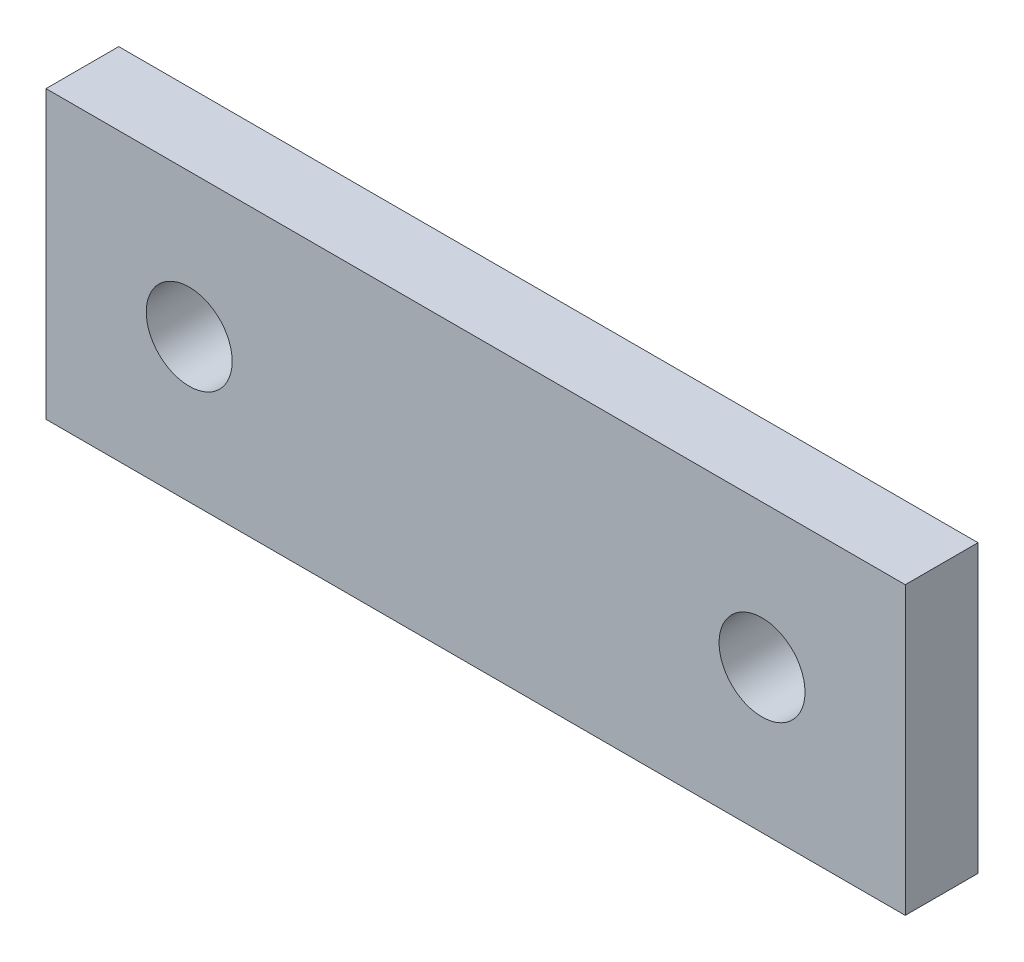
SolidWorks part; units mm, degrees
ref_plane "Front Plane" through (0, 0, 0) normal (0, 0, 1) x (1, 0, 0)
ref_plane "Top Plane" through (0, 0, 0) normal (0, 1, 0) x (1, 0, 0)
ref_plane "Right Plane" through (0, 0, 0) normal (1, 0, 0) x (0, 0, -1)
sketch "Sketch1" plane through (0, 0, 0) normal (0, 0, 1) x (1, 0, 0)
  line L1 (-31.6562, 6.35) -> (-1.6562, 6.35)
  line L2 (-31.6562, 6.35) -> (-31.6562, -3.65)
  line L3 (-31.6562, -3.65) -> (-1.6562, -3.65)
  line L4 (-1.6562, 6.35) -> (-1.6562, -3.65)
  circle A0 centre (-26.6562, 1.35) radius 1.5
  circle A1 centre (-6.6562, 1.35) radius 1.5
  dimension "D3" = 3
  dimension "D6" = 3
  dimension "D1" = 30
  dimension "D2" = 10
  dimension "D4" = 20
  dimension "D5" = 5
  dimension "D7" = 5
extrude "Boss-Extrude1" add sketch "Sketch1" along normal blind 2.54
